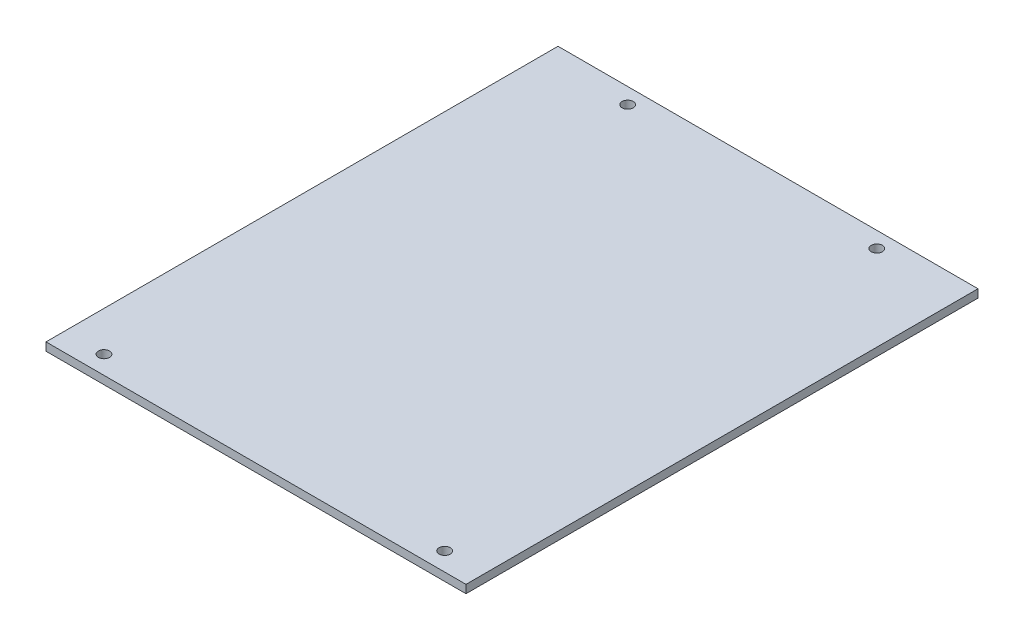
SolidWorks part; units mm, degrees
material "電力回路基板"
ref_plane "Front Plane" through (0, 0, 0) normal (0, 0, 1) x (1, 0, 0)
ref_plane "Top Plane" through (0, 0, 0) normal (0, 1, 0) x (1, 0, 0)
ref_plane "Right Plane" through (0, 0, 0) normal (1, 0, 0) x (0, 0, -1)
sketch "Sketch1" plane through (0, 0, 0) normal (0, 1, 0) x (1, 0, 0)
  line L0 (65.24, 10.5625) -> (65.24, -54.9375)
  line L1 (-17.76, 32.5625) -> (65.24, 32.5625)
  line L2 (65.24, 32.5625) -> (65.24, 10.5625)
  line L3 (-17.76, 19.3625) -> (-17.76, -46.1375)
  line L6 (65.24, -54.9375) -> (65.24, -68.1375)
  line L7 (65.24, -68.1375) -> (-17.76, -68.1375)
  line L8 (-17.76, -68.1375) -> (-17.76, -46.1375)
  line L11 (-17.76, 32.5625) -> (-17.76, 19.3625)
  dimension "D1" = 100.7
  dimension "D2" = 83
extrude "Boss-Extrude1" add sketch "Sketch1" along normal blind 1.6 contours L11 L3 L8 L7 L6 L0 L2 L1
hole_wizard "Ø2.2 (2.2) Diameter Hole2" positions "Sketch4" profile "Sketch2" hole size "Ø2.2" standard "ANSI Metric" end condition through all
sketch "Sketch4" plane through (0, 1.6, 0) normal (0, 1, 0) x (1, 0, 0)
  line L0 (-17.76, 32.5625) -> (65.24, 32.5625) construction
  line L1 (65.24, 32.5625) -> (65.24, -68.1375) construction
  line L2 (-17.76, -68.1375) -> (-17.76, 32.5625) construction
  point P0 (-0.76, 29.4625)
  point P2 (48.24, 29.4625)
  dimension "D1" = 3.1
  dimension "D2" = 17
  dimension "D3" = 17
sketch "Sketch2" plane through (-0.76, 1.6, -29.4625) normal (1, 0, 0) x (0, 0, 1)
  line L0 (0, 0) -> (0, 1.6)
  line L1 (0, 1.6) -> (1.1, 1.6)
  line L2 (1.1, 1.6) -> (1.1, 0)
  line L5 (1.1, 0) -> (0, 0)
  line L11 (0, -6.35) -> (0, 107.95) construction
  dimension "Thru Hole Dia." = 2.2
  dimension "Thru Hole Depth" = 1.6
hole_wizard "Ø2.2 (2.2) Diameter Hole1" positions "Sketch6" profile "Sketch5" hole size "Ø2.2" standard "ANSI Metric"
sketch "Sketch6" plane through (0, 1.6, 0) normal (0, 1, 0) x (1, 0, 0)
  line L0 (-17.76, -68.1375) -> (-17.76, 32.5625) construction
  line L1 (65.24, -68.1375) -> (-17.76, -68.1375) construction
  line L2 (65.24, 32.5625) -> (65.24, -68.1375) construction
  point P0 (-9.76, -64.5375)
  point P2 (57.24, -64.5375)
  dimension "D1" = 8
  dimension "D2" = 8
  dimension "D3" = 3.6
sketch "Sketch5" plane through (-9.76, 1.6, 64.5375) normal (1, 0, 0) x (0, 0, 1)
  line L0 (0, 0) -> (0, 2)
  line L1 (0, 2) -> (1.1, 2)
  line L2 (1.1, 2) -> (1.1, 0)
  line L5 (1.1, 0) -> (0, 0)
  line L10 (0, 2) -> (-1.1, 2) construction
  line L11 (0, -6.35) -> (0, 107.95) construction
  dimension "Hole Dia." = 2.2
  dimension "Hole Depth" = 2
  dimension "Drill Angle" = 180
sketch "Sketch7" plane through (0, 0, 0) normal (0, -1, 0) x (1, 0, 0)
  line L0 (-17.76, -32.5625) -> (65.24, -32.5625) construction
  line L1 (-17.76, 68.1375) -> (-17.56, 68.1375)
  line L2 (-17.76, 68.1375) -> (-17.76, -32.5625)
  line L3 (-17.76, -32.5625) -> (-17.56, -32.5625)
  line L4 (-17.56, 68.1375) -> (-17.56, -32.5625)
  line L6 (65.24, 68.1375) -> (65.04, 68.1375)
  line L7 (65.24, 68.1375) -> (65.24, -32.5625)
  line L8 (65.24, -32.5625) -> (65.04, -32.5625)
  line L9 (65.04, 68.1375) -> (65.04, -32.5625)
  dimension "D1" = 0.2
  dimension "D2" = 0.2
extrude "Extrude1" cut sketch "Sketch7" against normal through all
